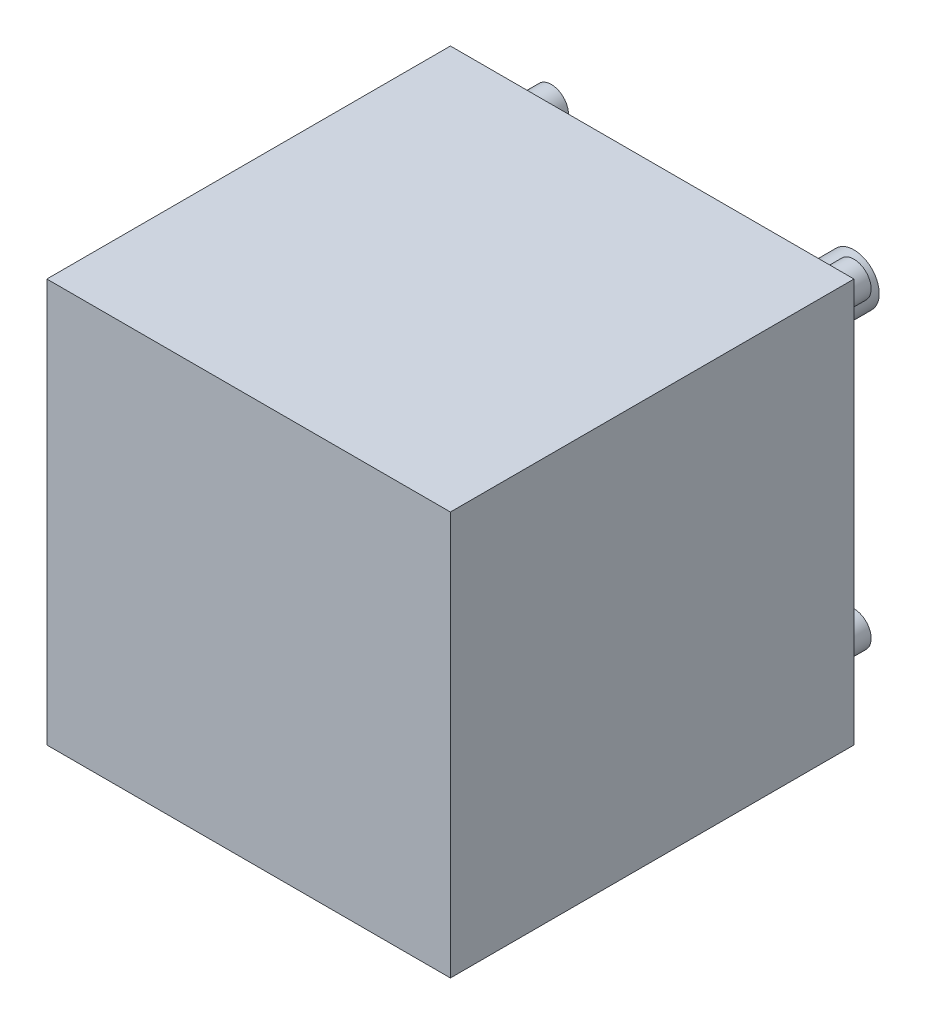
SolidWorks part; units mm, degrees
ref_plane "Front Plane" through (0, 0, 0) normal (0, 0, 1) x (1, 0, 0)
ref_plane "Top Plane" through (0, 0, 0) normal (0, 1, 0) x (1, 0, 0)
ref_plane "Right Plane" through (0, 0, 0) normal (1, 0, 0) x (0, 0, -1)
sketch "Sketch1" plane through (0, 0, 0) normal (0, 0, 1) x (1, 0, 0)
  line L1 (-20, -20) -> (20, -20)
  line L2 (-20, -20) -> (-20, 20)
  line L3 (-20, 20) -> (20, 20)
  line L4 (20, -20) -> (20, 20)
  line L5 (-20, -20) -> (20, 20) construction
  line L6 (-20, 20) -> (20, -20) construction
  point P0 (0, 0)
  dimension "D1" = 40
  dimension "D2" = 40
extrude "Boss-Extrude1" add sketch "Sketch1" along normal blind 40
sketch "Sketch2" plane through (0, 0, 0) normal (0, 0, -1) x (-1, 0, 0)
  line L0 (20, 20) -> (20, -20) construction
  line L2 (20, -20) -> (-20, -20) construction
  circle A0 centre (15, -15) radius 1.7
  dimension "D3" = 3.4
  dimension "D1" = 5
  dimension "D2" = 5
extrude "Boss-Extrude2" add sketch "Sketch2" along normal blind 5
mirror "Mirror1" about plane through (0, 0, 0) normal (1, 0, 0) of "Boss-Extrude2"
mirror "Mirror2" about plane through (0, 0, 0) normal (0, 1, 0) of "Mirror1", "Boss-Extrude2"
sketch "Sketch3" plane through (0, 0, 0) normal (0, 0, -1) x (-1, 0, 0)
  circle A0 centre (0, 0) radius 2.5
  dimension "D1" = 5
extrude "Boss-Extrude3" add sketch "Sketch3" along normal blind 20
equation "\"D1@Boss-Extrude2\" = \"mat@V1.assembly\""
